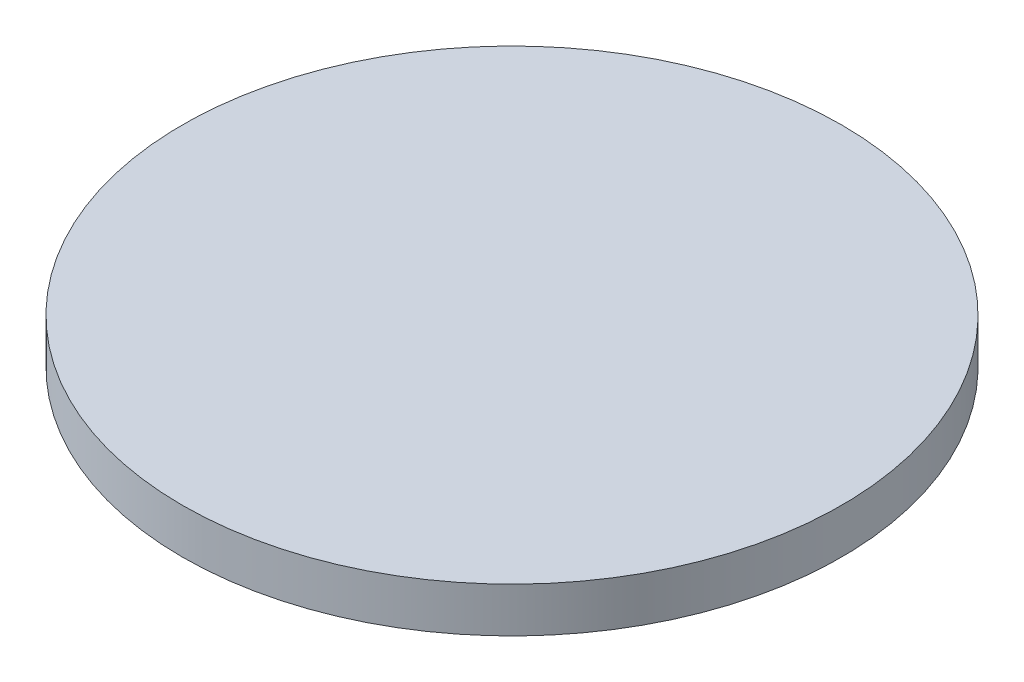
SolidWorks part; units mm, degrees
ref_plane "Front Plane" through (0, 0, 0) normal (0, 0, 1) x (1, 0, 0)
ref_plane "Top Plane" through (0, 0, 0) normal (0, 1, 0) x (1, 0, 0)
ref_plane "Right Plane" through (0, 0, 0) normal (1, 0, 0) x (0, 0, -1)
sketch "Sketch1" plane through (0, 0, 0) normal (0, 1, 0) x (1, 0, 0)
  circle A0 centre (0, 0) radius 23.5
extrude "Boss-Extrude1" add sketch "Sketch1" along normal blind 3.2
